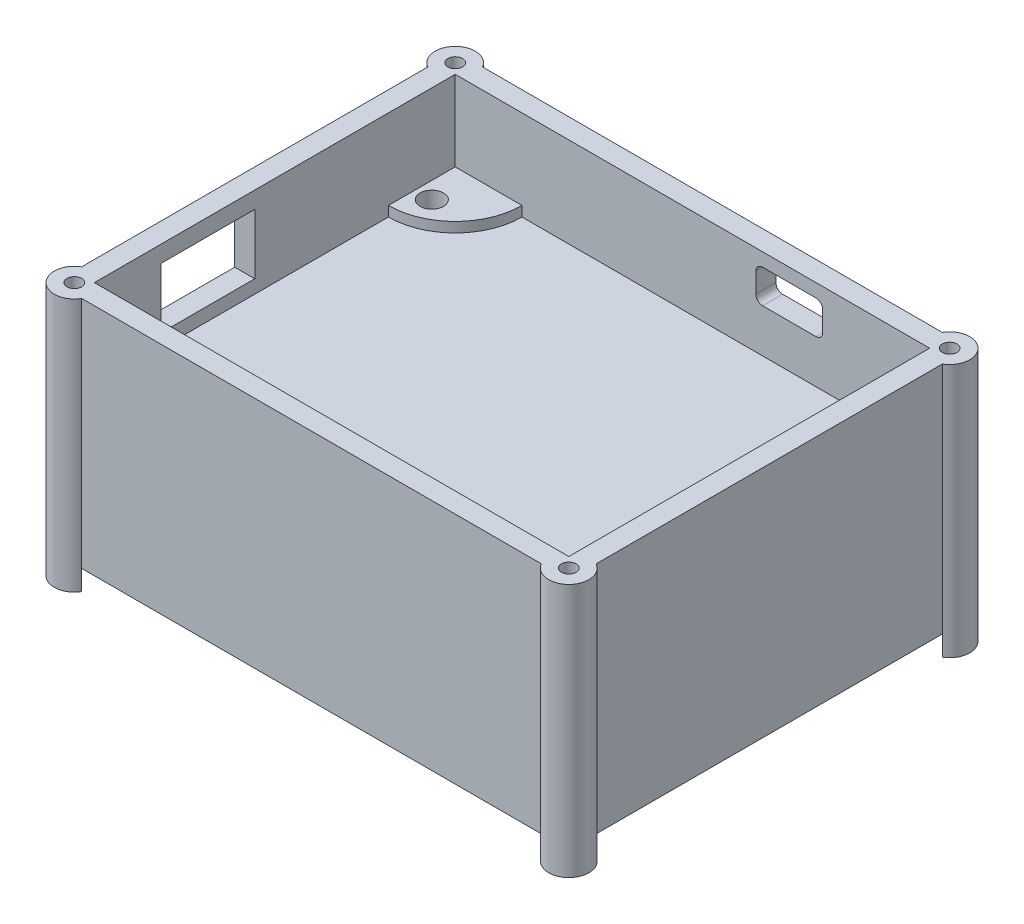
SolidWorks part; units mm, degrees
ref_plane "Front Plane" through (0, 0, 0) normal (0, 0, 1) x (1, 0, 0)
ref_plane "Top Plane" through (0, 0, 0) normal (0, 1, 0) x (1, 0, 0)
ref_plane "Right Plane" through (0, 0, 0) normal (1, 0, 0) x (0, 0, -1)
sketch "Sketch1" plane through (0, 0, 0) normal (0, 1, 0) x (1, 0, 0)
  line L0 (-40.1019, -26) -> (41.9426, -26) construction
  line L1 (-35.5, 27) -> (35.5, 27)
  line L2 (-35.5, 27) -> (-35.5, -27)
  line L3 (-35.5, -27) -> (35.5, -27)
  line L4 (35.5, 27) -> (35.5, -27)
  line L5 (-35.5, 27) -> (35.5, -27) construction
  line L6 (-35.5, -27) -> (35.5, 27) construction
  line L7 (-35, 28.4753) -> (-35, -32.1553) construction
  line L8 (35, 27.9594) -> (35, -29.4732) construction
  line L9 (-42.4046, 24) -> (57.0966, 24) construction
  line L11 (-38.5, 30) -> (38.5, 30)
  line L12 (-38.5, 30) -> (-38.5, -30)
  line L13 (-38.5, -30) -> (38.5, -30)
  line L14 (38.5, 30) -> (38.5, -30)
  line L15 (-38.5, 30) -> (38.5, -30) construction
  line L16 (-38.5, -30) -> (38.5, 30) construction
  circle A0 centre (-33, 21) radius 1.75
  circle A1 centre (33, 21) radius 1.75
  circle A2 centre (-33, -23) radius 1.75
  circle A3 centre (33, -23) radius 1.75
  arc A4 (-35.5, 17) -> (-25.5, 27) centre (-35.5, 27) ccw
  arc A5 (25.5, 27) -> (35.5, 17) centre (35.5, 27) ccw
  arc A6 (-25.5, -27) -> (-35.5, -17) centre (-35.5, -27) ccw
  arc A7 (35.5, -17) -> (25.5, -27) centre (35.5, -27) ccw
  point P0 (0, 0)
  point P22 (0, 0)
  dimension "D7" = 3.5
  dimension "D16" = 20
  dimension "D1" = 71
  dimension "D2" = 54
  dimension "D3" = 1
  dimension "D4" = 0.5
  dimension "D5" = 0.5
  dimension "D6" = 50
  dimension "D8" = 2
  dimension "D9" = 2
  dimension "D10" = 2
  dimension "D11" = 2
  dimension "D12" = 3
  dimension "D13" = 3
  dimension "D14" = 3
  dimension "D15" = 3
  dimension "D17" = 3
  dimension "D18" = 3
extrude "Boss-Extrude1" add sketch "Sketch1" along normal blind 45 contours L14 L11 L12 L13 L1 L4 L3 L2 | L3 A6 L2 A2 | L2 A4 L1 A0 | L1 A5 L4 A1 | L4 A7 L3 A3
sketch "Sketch2" plane through (0, 45, 0) normal (0, 1, 0) x (1, 0, 0)
  line L1 (-25.5, 27) -> (-35.5, 27)
  line L4 (-35.5, 27) -> (-35.5, 17)
  line L6 (35.5, 17) -> (35.5, 27)
  line L7 (35.5, 27) -> (25.5, 27)
  line L9 (-25.5, -27) -> (-35.5, -27)
  line L12 (-35.5, -27) -> (-35.5, -17)
  line L13 (25.5, -27) -> (35.5, -27)
  line L16 (35.5, -27) -> (35.5, -17)
  arc A0 (-25.5, -27) -> (-35.5, -17) centre (-35.5, -27) ccw construction
  arc A1 (35.5, -17) -> (25.5, -27) centre (35.5, -27) ccw construction
  arc A2 (25.5, 27) -> (35.5, 17) centre (35.5, 27) ccw construction
  arc A3 (-35.5, 17) -> (-25.5, 27) centre (-35.5, 27) ccw construction
  arc A4 (-25.5, -27) -> (-35.5, -17) centre (-35.5, -27) ccw
  arc A5 (35.5, -17) -> (25.5, -27) centre (35.5, -27) ccw
  arc A6 (25.5, 27) -> (35.5, 17) centre (35.5, 27) ccw
  arc A7 (-35.5, 17) -> (-25.5, 27) centre (-35.5, 27) ccw
  circle A8 centre (33, -23) radius 1.75 construction
  circle A9 centre (33, 21) radius 1.75 construction
  circle A10 centre (-33, 21) radius 1.75 construction
  circle A11 centre (-33, -23) radius 1.75 construction
  circle A12 centre (33, -23) radius 1.75
  circle A13 centre (33, 21) radius 1.75
  circle A14 centre (-33, 21) radius 1.75
  circle A15 centre (-33, -23) radius 1.75
extrude "Cut-Extrude1" cut sketch "Sketch2" against normal blind 12
sketch "Sketch3" plane through (0, 0, 0) normal (0, -1, 0) x (1, 0, 0)
  line L1 (-38.5, 30) -> (38.5, 30)
  line L2 (-38.5, 30) -> (-38.5, -30)
  line L3 (-38.5, -30) -> (38.5, -30)
  line L4 (38.5, 30) -> (38.5, -30)
  circle A0 centre (33, -21) radius 1.75 construction
  circle A1 centre (-33, -21) radius 1.75 construction
  circle A2 centre (33, 23) radius 1.75 construction
  circle A3 centre (-33, 23) radius 1.75 construction
  circle A4 centre (33, -21) radius 1.75
  circle A5 centre (-33, -21) radius 1.75
  circle A6 centre (33, 23) radius 1.75
  circle A7 centre (-33, 23) radius 1.75
extrude "Boss-Extrude2" add sketch "Sketch3" against normal blind 3
sketch "Sketch4" plane through (0, 0, -30) normal (0, 0, -1) x (-1, 0, 0)
  line L0 (-40.3952, 33) -> (-11.7521, 33) construction
  line L1 (-18.5, 43) -> (-10.5, 43)
  line L2 (-19.5, 42) -> (-19.5, 39)
  line L3 (-18.5, 38) -> (-10.5, 38)
  line L4 (-9.5, 42) -> (-9.5, 39)
  line L5 (-35.5, 42.4566) -> (-35.5, 51.6816) construction
  line L6 (-35.5, 33) -> (-35.5, 45) construction
  arc A0 (-19.5, 39) -> (-18.5, 38) centre (-18.5, 39) ccw
  arc A1 (-10.5, 38) -> (-9.5, 39) centre (-10.5, 39) ccw
  arc A2 (-9.5, 42) -> (-10.5, 43) centre (-10.5, 42) ccw
  arc A3 (-18.5, 43) -> (-19.5, 42) centre (-18.5, 42) ccw
  dimension "D5" = 1
  dimension "D1" = 10
  dimension "D2" = 16
  dimension "D3" = 10
  dimension "D4" = 5
extrude "Cut-Extrude2" cut sketch "Sketch4" against normal blind 10
sketch "Sketch6" plane through (-38.5, 0, 0) normal (-1, 0, 0) x (0, 0, 1)
  line L0 (27, 33) -> (-15.3654, 33) construction
  line L1 (17, 42.5) -> (3, 42.5)
  line L2 (17, 42.5) -> (17, 33.5)
  line L3 (17, 33.5) -> (3, 33.5)
  line L4 (3, 42.5) -> (3, 33.5)
  line L5 (27, 33) -> (27, 47.5269) construction
  dimension "D1" = 9
  dimension "D2" = 0.5
  dimension "D3" = 14
  dimension "D4" = 10
extrude "Cut-Extrude3" cut sketch "Sketch6" against normal blind 10
sketch "Sketch7" plane through (0, 45, 0) normal (0, 1, 0) x (1, 0, 0)
  line L0 (-38.5, 30) -> (38.5, 30) construction
  line L1 (-38.5, 30) -> (-38.5, -30) construction
  line L2 (38.5, 30) -> (38.5, -30) construction
  line L3 (-38.5, -30) -> (38.5, -30) construction
  circle A0 centre (-37, 28.5) radius 1.1
  circle A1 centre (37, 28.5) radius 1.1
  circle A2 centre (37, -28.5) radius 1.1
  circle A3 centre (-37, -28.5) radius 1.1
  dimension "D9" = 2.2
  dimension "D1" = 1.5
  dimension "D2" = 1.5
  dimension "D3" = 1.5
  dimension "D4" = 1.5
  dimension "D5" = 1.5
  dimension "D6" = 1.5
  dimension "D7" = 1.5
  dimension "D8" = 1.5
extrude "Cut-Extrude4" cut sketch "Sketch7" against normal blind 10
sketch "Sketch9" plane through (-38.5, 0, 0) normal (-1, 0, 0) x (0, 0, 1)
  line L0 (30, 45) -> (30, 0) construction
  line L1 (-30, 0) -> (30, 0)
  line L2 (-30, 0) -> (-30, 30)
  line L3 (-30, 30) -> (30, 30)
  line L4 (30, 0) -> (30, 30)
  line L5 (-27, 33) -> (-17, 33) construction
  dimension "D1" = 3
extrude "Cut-Extrude5" cut sketch "Sketch9" against normal blind 169
sketch "Sketch10" plane through (0, 30, 0) normal (0, -1, 0) x (1, 0, 0)
  line L1 (-38.5, 30) -> (38.5, 30)
  line L2 (-38.5, 30) -> (-38.5, -30)
  line L3 (-38.5, -30) -> (38.5, -30)
  line L4 (38.5, 30) -> (38.5, -30)
  line L5 (-35.5, 27) -> (35.5, 27)
  line L6 (-35.5, 27) -> (-35.5, -27)
  line L7 (-35.5, -27) -> (35.5, -27)
  line L8 (35.5, 27) -> (35.5, -27)
  line L9 (-35.5, 27) -> (35.5, -27) construction
  line L10 (-35.5, -27) -> (35.5, 27) construction
  point P6 (0, 0)
  line M13 (38.5, -30) -> (38.5, 30)
  line M14 (38.5, 30) -> (-38.5, 30)
  line M15 (-38.5, 30) -> (-38.5, -30)
  line M16 (-38.5, -30) -> (38.5, -30)
  line M18 (25.5, -27) -> (-25.5, -27)
  line M20 (-35.5, -17) -> (-35.5, 17)
  line M22 (-25.5, 27) -> (25.5, 27)
  line M24 (35.5, 17) -> (35.5, -17)
  dimension "D1" = 3
  dimension "D2" = 3
extrude "Boss-Extrude3" add sketch "Sketch10" along normal blind 20 contours L5 L8 L7 L6 M16 M13 M14 M15 M24 M18 M20 M22
sketch "Sketch11" plane through (0, 30, 0) normal (0, -1, 0) x (1, 0, 0)
  line L0 (35.5, 27) -> (35.5, -27) construction
  line L1 (-35.5, -27) -> (35.5, -27) construction
  line L2 (-35.5, 27) -> (-35.5, -27) construction
  line L3 (-35.5, 27) -> (35.5, 27) construction
  line L4 (35.5, 17) -> (35.5, -17)
  line L5 (-25.5, -27) -> (25.5, -27)
  line L6 (-35.5, 17) -> (-35.5, -17)
  line L7 (-25.5, 27) -> (25.5, 27)
  arc A0 (25.5, 27) -> (35.5, 17) centre (35.5, 27) ccw construction
  arc A1 (35.5, -17) -> (25.5, -27) centre (35.5, -27) ccw construction
  arc A2 (-25.5, -27) -> (-35.5, -17) centre (-35.5, -27) ccw construction
  arc A3 (-35.5, 17) -> (-25.5, 27) centre (-35.5, 27) ccw construction
  arc A4 (25.5, 27) -> (35.5, 17) centre (35.5, 27) ccw
  arc A5 (35.5, -17) -> (25.5, -27) centre (35.5, -27) ccw
  arc A6 (-25.5, -27) -> (-35.5, -17) centre (-35.5, -27) ccw
  arc A7 (-35.5, 17) -> (-25.5, 27) centre (-35.5, 27) ccw
extrude "Boss-Extrude4" add sketch "Sketch11" against normal blind 1.5
sketch "Sketch13" plane through (0, 30, 0) normal (0, -1, 0) x (1, 0, 0)
  circle A0 centre (22.5359, 21.7315) radius 3
  dimension "D1" = 6
extrude "Cut-Extrude6" cut sketch "Sketch13" against normal blind 1.5 contours A0
fillet "Fillet1" radius 1 4 edges at (-38.5, 27.5, 30) (38.5, 27.5, 30) (-38.5, 27.5, -30) (38.5, 27.5, -30)
sketch "Sketch14" plane through (0, 45, 0) normal (0, 1, 0) x (1, 0, 0)
  line L0 (-38.5, 29) -> (-38.5, -29) construction
  line L1 (-37.5, 30) -> (37.5, 30) construction
  line L2 (-38.5, 29) -> (-38.5, 25.9019)
  line L3 (-37.5, 30) -> (-34.4019, 30)
  arc A0 (-34.4019, 30) -> (-38.5, 25.9019) centre (-37, 28.5) ccw
  arc A1 (-37.5, 30) -> (-38.5, 29) centre (-37.5, 29) ccw construction
  arc A2 (-37.5, 30) -> (-38.5, 29) centre (-37.5, 29) ccw
  dimension "D1" = 6
extrude "Boss-Extrude5" add sketch "Sketch14" against normal blind 38
sketch "Sketch15" plane through (0, 45, 0) normal (0, 1, 0) x (1, 0, 0)
  line L0 (34.4019, -30) -> (37.5, -30)
  line L1 (38.5, 25.9019) -> (38.5, 29)
  line L4 (-38.5, 25.9019) -> (-38.5, -29)
  line L5 (-37.5, -30) -> (37.5, -30)
  line L6 (38.5, -29) -> (38.5, 29)
  line L7 (37.5, 30) -> (-34.4019, 30)
  line L8 (-38.5, -25.9019) -> (-38.5, -29)
  line L9 (-37.5, -30) -> (-34.4019, -30)
  line L10 (38.5, -29) -> (38.5, -25.9019)
  line L11 (37.5, 30) -> (34.4019, 30)
  arc A0 (38.5, 25.9019) -> (34.4019, 30) centre (37, 28.5) ccw
  arc A1 (34.4019, -30) -> (38.5, -25.9019) centre (37, -28.5) ccw
  arc A2 (-38.5, -25.9019) -> (-34.4019, -30) centre (-37, -28.5) ccw
  arc A4 (-34.4019, 30) -> (-38.5, 25.9019) centre (-37, 28.5) ccw
  arc A5 (-38.5, -29) -> (-37.5, -30) centre (-37.5, -29) ccw
  arc A6 (37.5, -30) -> (38.5, -29) centre (37.5, -29) ccw
  arc A7 (38.5, 29) -> (37.5, 30) centre (37.5, 29) ccw
  arc A8 (-34.4019, 30) -> (-38.5, 25.9019) centre (-37, 28.5) ccw
  arc A9 (-38.5, -29) -> (-37.5, -30) centre (-37.5, -29) ccw
  arc A10 (37.5, -30) -> (38.5, -29) centre (37.5, -29) ccw
  arc A11 (38.5, 29) -> (37.5, 30) centre (37.5, 29) ccw
  line M11 (-38.5, 25.9019) -> (-38.5, -29)
  arc M12 (-38.5, -29) -> (-37.5, -30) centre (-37.5, -29) ccw
  line M13 (-37.5, -30) -> (37.5, -30)
  arc M14 (37.5, -30) -> (38.5, -29) centre (37.5, -29) ccw
  line M15 (38.5, -29) -> (38.5, 29)
  arc M16 (38.5, 29) -> (37.5, 30) centre (37.5, 29) ccw
  line M17 (37.5, 30) -> (-34.4019, 30)
  dimension "D2" = 6
  dimension "D3" = 6
  dimension "D4" = 6
  dimension "D1" = 0
extrude "Boss-Extrude6" add sketch "Sketch15" against normal blind 38 contours A0 M15 M17 M16 | A1 M13 M15 M14 | A2 M11 M13 M12
